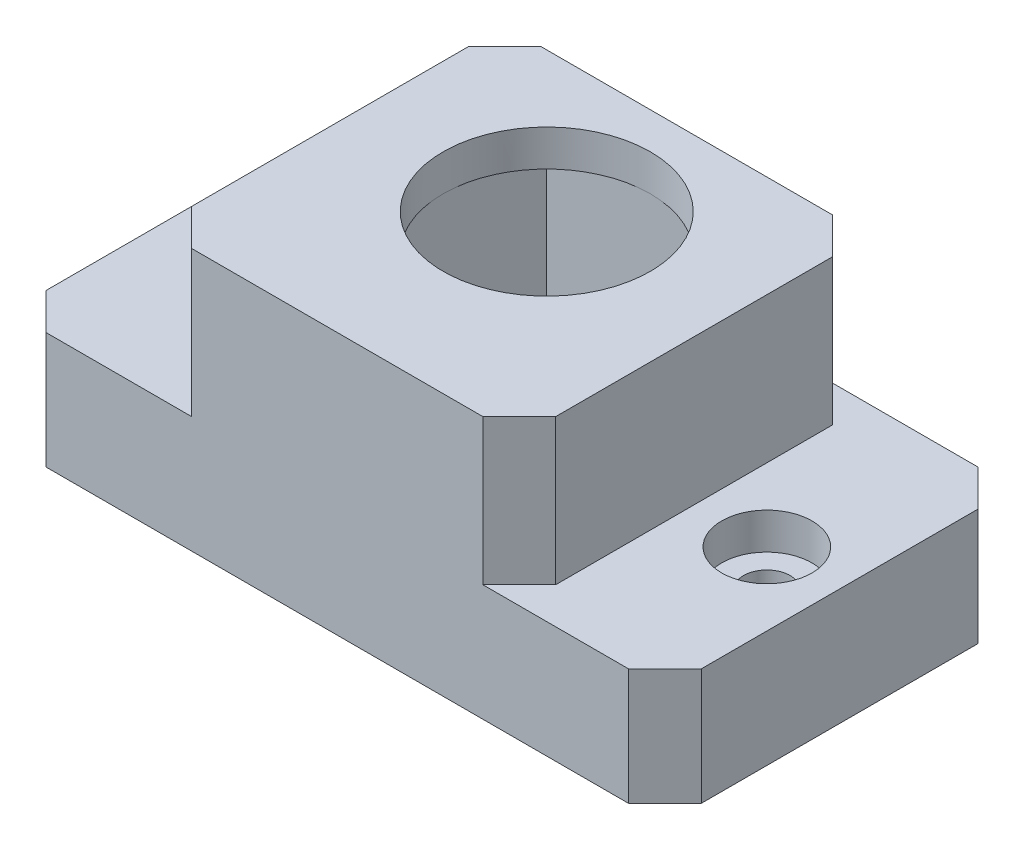
SolidWorks part; units mm, degrees
ref_plane "Front Plane" through (0, 0, 0) normal (0, 0, 1) x (1, 0, 0)
ref_plane "Top Plane" through (0, 0, 0) normal (0, 1, 0) x (1, 0, 0)
ref_plane "Right Plane" through (0, 0, 0) normal (1, 0, 0) x (0, 0, -1)
sketch "Sketch1" plane through (0, 0, 0) normal (0, 1, 0) x (1, 0, 0)
  line L1 (22.5, 12) -> (-22.5, 12)
  line L2 (22.5, 12) -> (22.5, -12)
  line L3 (22.5, -12) -> (-22.5, -12)
  line L4 (-22.5, 12) -> (-22.5, -12)
  line L5 (22.5, 12) -> (-22.5, -12) construction
  line L6 (22.5, -12) -> (-22.5, 12) construction
  point P0 (0, 0)
  dimension "D1" = 24
  dimension "D2" = 45
extrude "Boss-Extrude1" add sketch "Sketch1" along normal blind 18
sketch "Sketch2" plane through (0, 18, 0) normal (0, 1, 0) x (1, 0, 0)
  line L0 (-22.5, -12) -> (22.5, -12) construction
  line L1 (-22.5, 12) -> (-12.5, 12)
  line L2 (-22.5, 12) -> (-22.5, -12)
  line L3 (-22.5, -12) -> (-12.5, -12)
  line L4 (-12.5, 12) -> (-12.5, -12)
  line L6 (22.5, 12) -> (12.5, 12)
  line L7 (22.5, 12) -> (22.5, -12)
  line L8 (22.5, -12) -> (12.5, -12)
  line L9 (12.5, 12) -> (12.5, -12)
  dimension "D1" = 25
extrude "Cut-Extrude1" cut sketch "Sketch2" against normal offset from surface (10 mm away) 8 up to face at (0, 0, 0)
sketch "Sketch3" plane through (0, 8, 0) normal (0, 1, 0) x (1, 0, 0)
  line L0 (-22.5, 12) -> (-12.5, -12) construction
  line L1 (12.5, -12) -> (22.5, 12) construction
  circle A0 centre (-17.5, 0) radius 1.6
  circle A1 centre (17.5, 0) radius 1.6
  dimension "D1" = 3.2
extrude "Cut-Extrude2" cut sketch "Sketch3" against normal through all
sketch "Sketch4" plane through (0, 8, 0) normal (0, 1, 0) x (1, 0, 0)
  circle A0 centre (-17.5, 0) radius 3.1
  circle A1 centre (17.5, 0) radius 3.1
  dimension "D1" = 6.2
extrude "Cut-Extrude3" cut sketch "Sketch4" against normal blind 2.5
sketch "Sketch5" plane through (0, 0, 0) normal (0, -1, 0) x (1, 0, 0)
  line L0 (0, -12) -> (0, -9.5) construction
  line L1 (7.115, -9.5) -> (-7.115, -9.5)
  line L2 (7.115, -9.5) -> (7.115, 9.5)
  line L3 (7.115, 9.5) -> (-7.115, 9.5)
  line L4 (-7.115, -9.5) -> (-7.115, 9.5)
  line L5 (22.5, -12) -> (-22.5, -12) construction
  line L6 (7.115, -9.5) -> (-7.115, 4.73) construction
  line L7 (7.115, -9.5) -> (-7.115, -9.5) construction
  line L8 (7.115, -9.5) -> (7.115, 4.73) construction
  line L9 (7.115, 4.73) -> (-7.115, 4.73) construction
  line L10 (-7.115, -9.5) -> (-7.115, 4.73) construction
  dimension "D1" = 14.23
  dimension "D2" = 2.5
  dimension "D3" = 19
  dimension "D4" = 14.23
extrude "Cut-Extrude4" cut sketch "Sketch5" against normal offset from surface (15.5 mm away) 2.5 contours L4 L1 L2 L3 up to face at (0, 18, 0)
sketch "Sketch6" plane through (0, 15.5, 0) normal (0, -1, 0) x (1, 0, 0)
  line L0 (-7.115, -9.5) -> (-7.115, 9.5) construction
  line L1 (7.115, -9.5) -> (-7.115, -9.5)
  line L2 (7.115, -9.5) -> (7.115, 4.73)
  line L3 (7.115, 4.73) -> (-7.115, 4.73)
  line L4 (-7.115, -9.5) -> (-7.115, 4.73)
  line L5 (7.115, -9.5) -> (-7.115, 4.73) construction
  circle A0 centre (0, -2.385) radius 7.115
  dimension "D1" = 14.23
extrude "Cut-Extrude5" cut sketch "Sketch6" against normal through all contours A0
chamfer "Chamfer1" distance 2.5 angle 45 8 edges at (12.5, 13, 12) (-12.5, 13, 12) (-12.5, 13, -12) (12.5, 13, -12) (22.5, 4, 12) (-22.5, 4, 12) (-22.5, 4, -12) (22.5, 4, -12)
